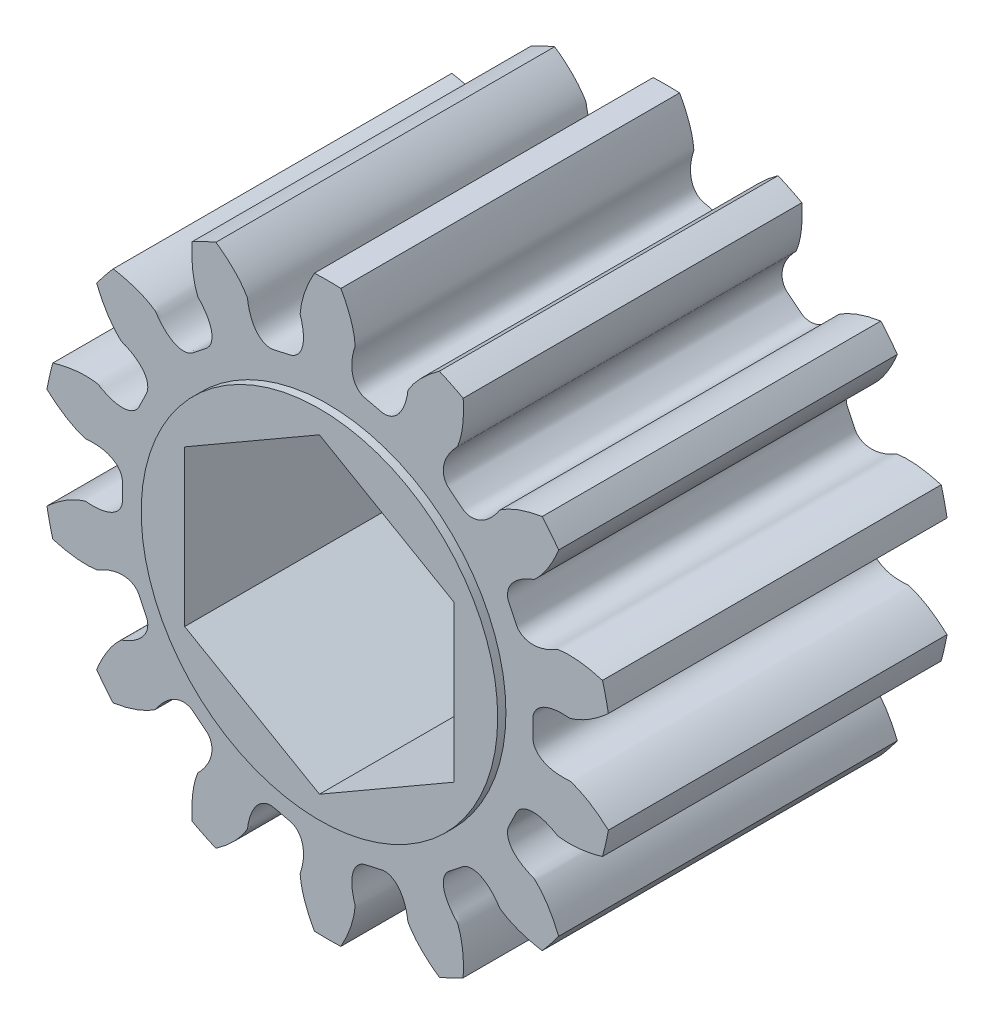
SolidWorks part; units mm, degrees
material "7075-T6 (SN)"
ref_plane "Front Plane" through (0, 0, 0) normal (0, 0, 1) x (1, 0, 0)
ref_plane "Top Plane" through (0, 0, 0) normal (0, 1, 0) x (1, 0, 0)
ref_plane "Right Plane" through (0, 0, 0) normal (1, 0, 0) x (0, 0, -1)
ref_plane "Plane1" through (0, 0, 6.0325) normal (0, 0, 1) x (1, 0, 0)
sketch "Sketch1" plane through (0, 0, 6.0325) normal (0, 0, 1) x (1, 0, 0)
  arc A0 (8.2288, 5.9593) -> (7.6409, 6.6964) centre (0, 0) ccw
  arc A1 (4.8282, 8.9394) -> (3.9788, 9.3485) centre (0, 0) ccw
  arc A2 (0.4714, 10.1491) -> (-0.4714, 10.1491) centre (0, 0) ccw
  arc A3 (-3.9788, 9.3485) -> (-4.8282, 8.9394) centre (0, 0) ccw
  arc A4 (-7.6409, 6.6964) -> (-8.2288, 5.9593) centre (0, 0) ccw
  arc A5 (-9.7897, 2.718) -> (-9.9995, 1.7988) centre (0, 0) ccw
  arc A6 (-9.9995, -1.7988) -> (-9.7897, -2.718) centre (0, 0) ccw
  arc A7 (-8.2288, -5.9593) -> (-7.6409, -6.6964) centre (0, 0) ccw
  arc A8 (-4.8282, -8.9394) -> (-3.9788, -9.3485) centre (0, 0) ccw
  arc A9 (-0.4714, -10.1491) -> (0.4714, -10.1491) centre (0, 0) ccw
  arc A10 (3.9788, -9.3485) -> (4.8282, -8.9394) centre (0, 0) ccw
  arc A11 (7.6409, -6.6964) -> (8.2288, -5.9593) centre (0, 0) ccw
  arc A12 (9.7897, -2.718) -> (9.9995, -1.7988) centre (0, 0) ccw
  arc A13 (9.9995, 1.7988) -> (9.7897, 2.718) centre (0, 0) ccw
  spline S0 degree 3 poles (8.2288, 5.9593) (8.1962, 5.8786) (8.1413, 5.7514) (8.0599, 5.5829) (7.9923, 5.4536) (7.9249, 5.3342) (7.8584, 5.2246) (7.7932, 5.1246) (7.7299, 5.0339) (7.669, 4.9525) (7.611, 4.8799) (7.5566, 4.8159) (7.506, 4.7604) (7.46, 4.7125) (7.4078, 4.6637) (7.3421, 4.5941) (7.241, 4.5723) (7.157, 4.5317) (7.0903, 4.5003) (7.0269, 4.467) (6.9663, 4.4327) (6.9087, 4.3974) (6.8539, 4.3609) (6.802, 4.3235) (6.7528, 4.2849) (6.7065, 4.2452) (6.663, 4.2044) (6.6223, 4.1622) (6.5843, 4.1185) (6.5492, 4.0731) (6.517, 4.0258) (6.4878, 3.9762) (6.4621, 3.9239) (6.4402, 3.8685) (6.4228, 3.8096) (6.4108, 3.7469) (6.4056, 3.6806) (6.4084, 3.6111) (6.4206, 3.5398) (6.4414, 3.4752) (6.4969, 3.3522) (6.5962, 3.1766) (6.6716, 2.9894) (6.7331, 2.8693) (6.7707, 2.8128) (6.8189, 2.7588) (6.8714, 2.7132) (6.9266, 2.676) (6.983, 2.6463) (7.0399, 2.6232) (7.0969, 2.6058) (7.1538, 2.5933) (7.2107, 2.5851) (7.2678, 2.5808) (7.3252, 2.58) (7.383, 2.5824) (7.4414, 2.588) (7.5005, 2.5965) (7.5604, 2.608) (7.6212, 2.6223) (7.6829, 2.6396) (7.7455, 2.6597) (7.8091, 2.6827) (7.8736, 2.7087) (7.9391, 2.7375) (8.0053, 2.77) (8.0894, 2.8104) (8.1695, 2.8759) (8.2649, 2.8839) (8.3356, 2.8943) (8.4017, 2.9003) (8.4767, 2.9053) (8.5607, 2.908) (8.6535, 2.908) (8.7552, 2.9048) (8.8655, 2.8978) (8.9844, 2.8865) (9.1115, 2.8702) (9.2469, 2.8484) (9.3901, 2.8206) (9.5727, 2.7791) (9.7064, 2.7428) (9.7897, 2.718) knots 0.010313 0.010313 0.010313 0.010313 0.046086 0.06731 0.087322 0.10612 0.123706 0.140079 0.155239 0.169186 0.18192 0.193442 0.203751 0.212847 0.22073 0.233282 0.251264 0.261667 0.271772 0.281588 0.291125 0.300395 0.30941 0.318185 0.326739 0.335092 0.343269 0.3513 0.35922 0.367069 0.374898 0.382761 0.390725 0.398861 0.407247 0.415956 0.425052 0.434567 0.444491 0.454753 0.462386 0.5 0.537614 0.545247 0.555509 0.565433 0.574948 0.584044 0.592753 0.601139 0.609275 0.617239 0.625102 0.632931 0.64078 0.6487 0.656731 0.664908 0.673261 0.681815 0.69059 0.699605 0.708875 0.718412 0.728228 0.738333 0.748736 0.766718 0.77927 0.787153 0.796249 0.806558 0.81808 0.830814 0.844761 0.859921 0.876294 0.89388 0.912678 0.93269 0.953914 0.989687 0.989687 0.989687 0.989687
  spline S1 degree 3 poles (4.8282, 8.9394) (4.8339, 8.8527) (4.8396, 8.7142) (4.8394, 8.5271) (4.8346, 8.3812) (4.8257, 8.2444) (4.8133, 8.1168) (4.7979, 7.9984) (4.7802, 7.8893) (4.7607, 7.7895) (4.74, 7.699) (4.7187, 7.6177) (4.6972, 7.5457) (4.6765, 7.4825) (4.6507, 7.4159) (4.6217, 7.3247) (4.54, 7.2612) (4.482, 7.1882) (4.4355, 7.1309) (4.3929, 7.0734) (4.3531, 7.0163) (4.3165, 6.9594) (4.283, 6.9029) (4.2525, 6.8466) (4.2249, 6.7905) (4.2004, 6.7347) (4.179, 6.679) (4.1606, 6.6233) (4.1453, 6.5675) (4.1333, 6.5113) (4.1248, 6.4547) (4.1201, 6.3974) (4.1196, 6.3391) (4.1239, 6.2797) (4.1338, 6.2191) (4.1502, 6.1574) (4.1743, 6.0954) (4.2069, 6.034) (4.2489, 5.975) (4.2956, 5.9259) (4.3991, 5.8391) (4.5647, 5.7239) (4.7138, 5.5881) (4.8214, 5.5066) (4.8797, 5.4719) (4.9466, 5.4441) (5.0137, 5.4259) (5.0795, 5.4163) (5.1433, 5.4141) (5.2046, 5.4179) (5.2634, 5.4269) (5.3202, 5.4404) (5.375, 5.4577) (5.4283, 5.4786) (5.4804, 5.5028) (5.5314, 5.5301) (5.5816, 5.5604) (5.6312, 5.5937) (5.6801, 5.6301) (5.7287, 5.6693) (5.7767, 5.7116) (5.8244, 5.7569) (5.8717, 5.8053) (5.9186, 5.8567) (5.9652, 5.9111) (6.0107, 5.9691) (6.0689, 6.042) (6.1127, 6.1357) (6.1951, 6.1843) (6.2543, 6.2243) (6.3113, 6.2585) (6.3767, 6.2955) (6.4512, 6.3343) (6.5348, 6.3747) (6.6278, 6.4159) (6.7302, 6.4575) (6.8422, 6.4988) (6.9639, 6.5393) (7.0953, 6.5784) (7.2364, 6.6155) (7.4188, 6.6573) (7.5551, 6.6826) (7.6409, 6.6964) knots 0.010313 0.010313 0.010313 0.010313 0.046086 0.06731 0.087322 0.10612 0.123706 0.140079 0.155239 0.169186 0.18192 0.193442 0.203751 0.212847 0.22073 0.233282 0.251264 0.261667 0.271772 0.281588 0.291125 0.300395 0.30941 0.318185 0.326739 0.335092 0.343269 0.3513 0.35922 0.367069 0.374898 0.382761 0.390725 0.398861 0.407247 0.415956 0.425052 0.434567 0.444491 0.454753 0.462386 0.5 0.537614 0.545247 0.555509 0.565433 0.574948 0.584044 0.592753 0.601139 0.609275 0.617239 0.625102 0.632931 0.64078 0.6487 0.656731 0.664908 0.673261 0.681815 0.69059 0.699605 0.708875 0.718412 0.728228 0.738333 0.748736 0.766718 0.77927 0.787153 0.796249 0.806558 0.81808 0.830814 0.844761 0.859921 0.876294 0.89388 0.912678 0.93269 0.953914 0.989687 0.989687 0.989687 0.989687
  spline S2 degree 3 poles (0.4714, 10.1491) (0.5141, 10.0733) (0.5793, 9.9511) (0.6604, 9.7823) (0.7193, 9.6489) (0.7707, 9.5218) (0.8149, 9.4014) (0.8524, 9.2881) (0.8838, 9.1821) (0.9095, 9.0837) (0.9301, 8.9931) (0.9462, 8.9106) (0.9581, 8.8365) (0.9669, 8.7706) (0.9725, 8.6994) (0.9859, 8.6046) (0.9399, 8.512) (0.9192, 8.421) (0.9023, 8.3492) (0.8888, 8.2789) (0.8778, 8.2102) (0.8695, 8.1431) (0.8638, 8.0776) (0.8607, 8.0136) (0.8602, 7.9512) (0.8624, 7.8903) (0.8672, 7.8307) (0.8748, 7.7726) (0.8853, 7.7157) (0.8988, 7.6599) (0.9158, 7.6052) (0.9364, 7.5515) (0.9612, 7.4988) (0.9909, 7.4471) (1.0261, 7.3968) (1.0676, 7.3484) (1.1162, 7.3029) (1.1722, 7.2618) (1.2357, 7.2268) (1.2991, 7.2028) (1.4299, 7.1695) (1.6291, 7.1376) (1.8224, 7.08) (1.9547, 7.0532) (2.0223, 7.0473) (2.0946, 7.0513) (2.163, 7.064) (2.2265, 7.0839) (2.2849, 7.1095) (2.3384, 7.1395) (2.3875, 7.1732) (2.4328, 7.21) (2.4747, 7.2494) (2.5137, 7.2913) (2.5501, 7.3357) (2.5842, 7.3824) (2.6163, 7.4315) (2.6465, 7.4831) (2.6748, 7.537) (2.7015, 7.5935) (2.7265, 7.6524) (2.7498, 7.7139) (2.7714, 7.778) (2.7913, 7.8447) (2.8097, 7.9139) (2.8255, 7.9859) (2.8464, 8.0769) (2.8451, 8.1803) (2.8983, 8.2598) (2.9343, 8.3216) (2.9708, 8.3771) (3.0137, 8.4388) (3.0639, 8.5061) (3.1218, 8.5787) (3.1877, 8.6562) (3.2619, 8.7381) (3.3449, 8.8239) (3.437, 8.9132) (3.5384, 9.0054) (3.6494, 9.1001) (3.7956, 9.217) (3.9074, 9.2988) (3.9788, 9.3485) knots 0.010313 0.010313 0.010313 0.010313 0.046086 0.06731 0.087322 0.10612 0.123706 0.140079 0.155239 0.169186 0.18192 0.193442 0.203751 0.212847 0.22073 0.233282 0.251264 0.261667 0.271772 0.281588 0.291125 0.300395 0.30941 0.318185 0.326739 0.335092 0.343269 0.3513 0.35922 0.367069 0.374898 0.382761 0.390725 0.398861 0.407247 0.415956 0.425052 0.434567 0.444491 0.454753 0.462386 0.5 0.537614 0.545247 0.555509 0.565433 0.574948 0.584044 0.592753 0.601139 0.609275 0.617239 0.625102 0.632931 0.64078 0.6487 0.656731 0.664908 0.673261 0.681815 0.69059 0.699605 0.708875 0.718412 0.728228 0.738333 0.748736 0.766718 0.77927 0.787153 0.796249 0.806558 0.81808 0.830814 0.844761 0.859921 0.876294 0.89388 0.912678 0.93269 0.953914 0.989687 0.989687 0.989687 0.989687
  spline S3 degree 3 poles (-3.9788, 9.3485) (-3.9074, 9.2988) (-3.7956, 9.217) (-3.6494, 9.1001) (-3.5384, 9.0054) (-3.437, 8.9132) (-3.3449, 8.8239) (-3.2619, 8.7381) (-3.1877, 8.6562) (-3.1218, 8.5787) (-3.0639, 8.5061) (-3.0137, 8.4388) (-2.9708, 8.3771) (-2.9343, 8.3216) (-2.8983, 8.2598) (-2.8451, 8.1803) (-2.8464, 8.0769) (-2.8255, 7.9859) (-2.8097, 7.9139) (-2.7913, 7.8447) (-2.7714, 7.778) (-2.7498, 7.7139) (-2.7265, 7.6524) (-2.7015, 7.5935) (-2.6748, 7.537) (-2.6465, 7.4831) (-2.6163, 7.4315) (-2.5842, 7.3824) (-2.5501, 7.3357) (-2.5137, 7.2913) (-2.4747, 7.2494) (-2.4328, 7.21) (-2.3875, 7.1732) (-2.3384, 7.1395) (-2.2849, 7.1095) (-2.2265, 7.0839) (-2.163, 7.064) (-2.0946, 7.0513) (-2.0223, 7.0473) (-1.9547, 7.0532) (-1.8224, 7.08) (-1.6291, 7.1376) (-1.4299, 7.1695) (-1.2991, 7.2028) (-1.2357, 7.2268) (-1.1722, 7.2618) (-1.1162, 7.3029) (-1.0676, 7.3484) (-1.0261, 7.3968) (-0.9909, 7.4471) (-0.9612, 7.4988) (-0.9364, 7.5515) (-0.9158, 7.6052) (-0.8988, 7.6599) (-0.8853, 7.7157) (-0.8748, 7.7726) (-0.8672, 7.8307) (-0.8624, 7.8903) (-0.8602, 7.9512) (-0.8607, 8.0136) (-0.8638, 8.0776) (-0.8695, 8.1431) (-0.8778, 8.2102) (-0.8888, 8.2789) (-0.9023, 8.3492) (-0.9192, 8.421) (-0.9399, 8.512) (-0.9859, 8.6046) (-0.9725, 8.6994) (-0.9669, 8.7706) (-0.9581, 8.8365) (-0.9462, 8.9106) (-0.9301, 8.9931) (-0.9095, 9.0837) (-0.8838, 9.1821) (-0.8524, 9.2881) (-0.8149, 9.4014) (-0.7707, 9.5218) (-0.7193, 9.6489) (-0.6604, 9.7823) (-0.5793, 9.9511) (-0.5141, 10.0733) (-0.4714, 10.1491) knots 0.010313 0.010313 0.010313 0.010313 0.046086 0.06731 0.087322 0.10612 0.123706 0.140079 0.155239 0.169186 0.18192 0.193442 0.203751 0.212847 0.22073 0.233282 0.251264 0.261667 0.271772 0.281588 0.291125 0.300395 0.30941 0.318185 0.326739 0.335092 0.343269 0.3513 0.35922 0.367069 0.374898 0.382761 0.390725 0.398861 0.407247 0.415956 0.425052 0.434567 0.444491 0.454753 0.462386 0.5 0.537614 0.545247 0.555509 0.565433 0.574948 0.584044 0.592753 0.601139 0.609275 0.617239 0.625102 0.632931 0.64078 0.6487 0.656731 0.664908 0.673261 0.681815 0.69059 0.699605 0.708875 0.718412 0.728228 0.738333 0.748736 0.766718 0.77927 0.787153 0.796249 0.806558 0.81808 0.830814 0.844761 0.859921 0.876294 0.89388 0.912678 0.93269 0.953914 0.989687 0.989687 0.989687 0.989687
  spline S4 degree 3 poles (-7.6409, 6.6964) (-7.5551, 6.6826) (-7.4188, 6.6573) (-7.2364, 6.6155) (-7.0953, 6.5784) (-6.9639, 6.5393) (-6.8422, 6.4988) (-6.7302, 6.4575) (-6.6278, 6.4159) (-6.5348, 6.3747) (-6.4512, 6.3343) (-6.3767, 6.2955) (-6.3113, 6.2585) (-6.2543, 6.2243) (-6.1951, 6.1843) (-6.1127, 6.1357) (-6.0689, 6.042) (-6.0107, 5.9691) (-5.9652, 5.9111) (-5.9186, 5.8567) (-5.8717, 5.8053) (-5.8244, 5.7569) (-5.7767, 5.7116) (-5.7287, 5.6693) (-5.6801, 5.6301) (-5.6312, 5.5937) (-5.5816, 5.5604) (-5.5314, 5.5301) (-5.4804, 5.5028) (-5.4283, 5.4786) (-5.375, 5.4577) (-5.3202, 5.4404) (-5.2634, 5.4269) (-5.2046, 5.4179) (-5.1433, 5.4141) (-5.0795, 5.4163) (-5.0137, 5.4259) (-4.9466, 5.4441) (-4.8797, 5.4719) (-4.8214, 5.5066) (-4.7138, 5.5881) (-4.5647, 5.7239) (-4.3991, 5.8391) (-4.2956, 5.9259) (-4.2489, 5.975) (-4.2069, 6.034) (-4.1743, 6.0954) (-4.1502, 6.1574) (-4.1338, 6.2191) (-4.1239, 6.2797) (-4.1196, 6.3391) (-4.1201, 6.3974) (-4.1248, 6.4547) (-4.1333, 6.5113) (-4.1453, 6.5675) (-4.1606, 6.6233) (-4.179, 6.679) (-4.2004, 6.7347) (-4.2249, 6.7905) (-4.2525, 6.8466) (-4.283, 6.9029) (-4.3165, 6.9594) (-4.3531, 7.0163) (-4.3929, 7.0734) (-4.4355, 7.1309) (-4.482, 7.1882) (-4.54, 7.2612) (-4.6217, 7.3247) (-4.6507, 7.4159) (-4.6765, 7.4825) (-4.6972, 7.5457) (-4.7187, 7.6177) (-4.74, 7.699) (-4.7607, 7.7895) (-4.7802, 7.8893) (-4.7979, 7.9984) (-4.8133, 8.1168) (-4.8257, 8.2444) (-4.8346, 8.3812) (-4.8394, 8.5271) (-4.8396, 8.7142) (-4.8339, 8.8527) (-4.8282, 8.9394) knots 0.010313 0.010313 0.010313 0.010313 0.046086 0.06731 0.087322 0.10612 0.123706 0.140079 0.155239 0.169186 0.18192 0.193442 0.203751 0.212847 0.22073 0.233282 0.251264 0.261667 0.271772 0.281588 0.291125 0.300395 0.30941 0.318185 0.326739 0.335092 0.343269 0.3513 0.35922 0.367069 0.374898 0.382761 0.390725 0.398861 0.407247 0.415956 0.425052 0.434567 0.444491 0.454753 0.462386 0.5 0.537614 0.545247 0.555509 0.565433 0.574948 0.584044 0.592753 0.601139 0.609275 0.617239 0.625102 0.632931 0.64078 0.6487 0.656731 0.664908 0.673261 0.681815 0.69059 0.699605 0.708875 0.718412 0.728228 0.738333 0.748736 0.766718 0.77927 0.787153 0.796249 0.806558 0.81808 0.830814 0.844761 0.859921 0.876294 0.89388 0.912678 0.93269 0.953914 0.989687 0.989687 0.989687 0.989687
  spline S5 degree 3 poles (-9.7897, 2.718) (-9.7064, 2.7428) (-9.5727, 2.7791) (-9.3901, 2.8206) (-9.2469, 2.8484) (-9.1115, 2.8702) (-8.9844, 2.8865) (-8.8655, 2.8978) (-8.7552, 2.9048) (-8.6535, 2.908) (-8.5607, 2.908) (-8.4767, 2.9053) (-8.4017, 2.9003) (-8.3356, 2.8943) (-8.2649, 2.8839) (-8.1695, 2.8759) (-8.0894, 2.8104) (-8.0053, 2.77) (-7.9391, 2.7375) (-7.8736, 2.7087) (-7.8091, 2.6827) (-7.7455, 2.6597) (-7.6829, 2.6396) (-7.6212, 2.6223) (-7.5604, 2.608) (-7.5005, 2.5965) (-7.4414, 2.588) (-7.383, 2.5824) (-7.3252, 2.58) (-7.2678, 2.5808) (-7.2107, 2.5851) (-7.1538, 2.5933) (-7.0969, 2.6058) (-7.0399, 2.6232) (-6.983, 2.6463) (-6.9266, 2.676) (-6.8714, 2.7132) (-6.8189, 2.7588) (-6.7707, 2.8128) (-6.7331, 2.8693) (-6.6716, 2.9894) (-6.5962, 3.1766) (-6.4969, 3.3522) (-6.4414, 3.4752) (-6.4206, 3.5398) (-6.4084, 3.6111) (-6.4056, 3.6806) (-6.4108, 3.7469) (-6.4228, 3.8096) (-6.4402, 3.8685) (-6.4621, 3.9239) (-6.4878, 3.9762) (-6.517, 4.0258) (-6.5492, 4.0731) (-6.5843, 4.1185) (-6.6223, 4.1622) (-6.663, 4.2044) (-6.7065, 4.2452) (-6.7528, 4.2849) (-6.802, 4.3235) (-6.8539, 4.3609) (-6.9087, 4.3974) (-6.9663, 4.4327) (-7.0269, 4.467) (-7.0903, 4.5003) (-7.157, 4.5317) (-7.241, 4.5723) (-7.3421, 4.5941) (-7.4078, 4.6637) (-7.46, 4.7125) (-7.506, 4.7604) (-7.5566, 4.8159) (-7.611, 4.8799) (-7.669, 4.9525) (-7.7299, 5.0339) (-7.7932, 5.1246) (-7.8584, 5.2246) (-7.9249, 5.3342) (-7.9923, 5.4536) (-8.0599, 5.5829) (-8.1413, 5.7514) (-8.1962, 5.8786) (-8.2288, 5.9593) knots 0.010313 0.010313 0.010313 0.010313 0.046086 0.06731 0.087322 0.10612 0.123706 0.140079 0.155239 0.169186 0.18192 0.193442 0.203751 0.212847 0.22073 0.233282 0.251264 0.261667 0.271772 0.281588 0.291125 0.300395 0.30941 0.318185 0.326739 0.335092 0.343269 0.3513 0.35922 0.367069 0.374898 0.382761 0.390725 0.398861 0.407247 0.415956 0.425052 0.434567 0.444491 0.454753 0.462386 0.5 0.537614 0.545247 0.555509 0.565433 0.574948 0.584044 0.592753 0.601139 0.609275 0.617239 0.625102 0.632931 0.64078 0.6487 0.656731 0.664908 0.673261 0.681815 0.69059 0.699605 0.708875 0.718412 0.728228 0.738333 0.748736 0.766718 0.77927 0.787153 0.796249 0.806558 0.81808 0.830814 0.844761 0.859921 0.876294 0.89388 0.912678 0.93269 0.953914 0.989687 0.989687 0.989687 0.989687
  spline S6 degree 3 poles (-9.9995, -1.7988) (-9.9352, -1.7403) (-9.8305, -1.6495) (-9.684, -1.5329) (-9.567, -1.4458) (-9.4545, -1.3674) (-9.347, -1.2976) (-9.2449, -1.2357) (-9.1485, -1.1816) (-9.0583, -1.1346) (-8.9746, -1.0943) (-8.8978, -1.0603) (-8.8281, -1.0323) (-8.7659, -1.009) (-8.6977, -0.9877) (-8.6083, -0.9535) (-8.5077, -0.9778) (-8.4144, -0.9777) (-8.3407, -0.9782) (-8.2691, -0.9757) (-8.1997, -0.9712) (-8.1324, -0.9643) (-8.0673, -0.9553) (-8.0042, -0.9441) (-7.9433, -0.9306) (-7.8843, -0.915) (-7.8274, -0.897) (-7.7724, -0.8767) (-7.7192, -0.8538) (-7.6679, -0.8282) (-7.6183, -0.7995) (-7.5705, -0.7674) (-7.5247, -0.7315) (-7.4809, -0.6911) (-7.4397, -0.6456) (-7.4017, -0.5943) (-7.3682, -0.5368) (-7.3406, -0.473) (-7.3206, -0.4034) (-7.3113, -0.3362) (-7.308, -0.2013) (-7.3212, 0) (-7.308, 0.2013) (-7.3113, 0.3362) (-7.3206, 0.4034) (-7.3406, 0.473) (-7.3682, 0.5368) (-7.4017, 0.5943) (-7.4397, 0.6456) (-7.4809, 0.6911) (-7.5247, 0.7315) (-7.5705, 0.7674) (-7.6183, 0.7995) (-7.6679, 0.8282) (-7.7192, 0.8538) (-7.7724, 0.8767) (-7.8274, 0.897) (-7.8843, 0.915) (-7.9433, 0.9306) (-8.0042, 0.9441) (-8.0673, 0.9553) (-8.1324, 0.9643) (-8.1997, 0.9712) (-8.2691, 0.9757) (-8.3407, 0.9782) (-8.4144, 0.9777) (-8.5077, 0.9778) (-8.6083, 0.9535) (-8.6977, 0.9877) (-8.7659, 1.009) (-8.8281, 1.0323) (-8.8978, 1.0603) (-8.9746, 1.0943) (-9.0583, 1.1346) (-9.1485, 1.1816) (-9.2449, 1.2357) (-9.347, 1.2976) (-9.4545, 1.3674) (-9.567, 1.4458) (-9.684, 1.5329) (-9.8305, 1.6495) (-9.9352, 1.7403) (-9.9995, 1.7988) knots 0.010313 0.010313 0.010313 0.010313 0.046086 0.06731 0.087322 0.10612 0.123706 0.140079 0.155239 0.169186 0.18192 0.193442 0.203751 0.212847 0.22073 0.233282 0.251264 0.261667 0.271772 0.281588 0.291125 0.300395 0.30941 0.318185 0.326739 0.335092 0.343269 0.3513 0.35922 0.367069 0.374898 0.382761 0.390725 0.398861 0.407247 0.415956 0.425052 0.434567 0.444491 0.454753 0.462386 0.5 0.537614 0.545247 0.555509 0.565433 0.574948 0.584044 0.592753 0.601139 0.609275 0.617239 0.625102 0.632931 0.64078 0.6487 0.656731 0.664908 0.673261 0.681815 0.69059 0.699605 0.708875 0.718412 0.728228 0.738333 0.748736 0.766718 0.77927 0.787153 0.796249 0.806558 0.81808 0.830814 0.844761 0.859921 0.876294 0.89388 0.912678 0.93269 0.953914 0.989687 0.989687 0.989687 0.989687
  spline S7 degree 3 poles (-8.2288, -5.9593) (-8.1962, -5.8786) (-8.1413, -5.7514) (-8.0599, -5.5829) (-7.9923, -5.4536) (-7.9249, -5.3342) (-7.8584, -5.2246) (-7.7932, -5.1246) (-7.7299, -5.0339) (-7.669, -4.9525) (-7.611, -4.8799) (-7.5566, -4.8159) (-7.506, -4.7604) (-7.46, -4.7125) (-7.4078, -4.6637) (-7.3421, -4.5941) (-7.241, -4.5723) (-7.157, -4.5317) (-7.0903, -4.5003) (-7.0269, -4.467) (-6.9663, -4.4327) (-6.9087, -4.3974) (-6.8539, -4.3609) (-6.802, -4.3235) (-6.7528, -4.2849) (-6.7065, -4.2452) (-6.663, -4.2044) (-6.6223, -4.1622) (-6.5843, -4.1185) (-6.5492, -4.0731) (-6.517, -4.0258) (-6.4878, -3.9762) (-6.4621, -3.9239) (-6.4402, -3.8685) (-6.4228, -3.8096) (-6.4108, -3.7469) (-6.4056, -3.6806) (-6.4084, -3.6111) (-6.4206, -3.5398) (-6.4414, -3.4752) (-6.4969, -3.3522) (-6.5962, -3.1766) (-6.6716, -2.9894) (-6.7331, -2.8693) (-6.7707, -2.8128) (-6.8189, -2.7588) (-6.8714, -2.7132) (-6.9266, -2.676) (-6.983, -2.6463) (-7.0399, -2.6232) (-7.0969, -2.6058) (-7.1538, -2.5933) (-7.2107, -2.5851) (-7.2678, -2.5808) (-7.3252, -2.58) (-7.383, -2.5824) (-7.4414, -2.588) (-7.5005, -2.5965) (-7.5604, -2.608) (-7.6212, -2.6223) (-7.6829, -2.6396) (-7.7455, -2.6597) (-7.8091, -2.6827) (-7.8736, -2.7087) (-7.9391, -2.7375) (-8.0053, -2.77) (-8.0894, -2.8104) (-8.1695, -2.8759) (-8.2649, -2.8839) (-8.3356, -2.8943) (-8.4017, -2.9003) (-8.4767, -2.9053) (-8.5607, -2.908) (-8.6535, -2.908) (-8.7552, -2.9048) (-8.8655, -2.8978) (-8.9844, -2.8865) (-9.1115, -2.8702) (-9.2469, -2.8484) (-9.3901, -2.8206) (-9.5727, -2.7791) (-9.7064, -2.7428) (-9.7897, -2.718) knots 0.010313 0.010313 0.010313 0.010313 0.046086 0.06731 0.087322 0.10612 0.123706 0.140079 0.155239 0.169186 0.18192 0.193442 0.203751 0.212847 0.22073 0.233282 0.251264 0.261667 0.271772 0.281588 0.291125 0.300395 0.30941 0.318185 0.326739 0.335092 0.343269 0.3513 0.35922 0.367069 0.374898 0.382761 0.390725 0.398861 0.407247 0.415956 0.425052 0.434567 0.444491 0.454753 0.462386 0.5 0.537614 0.545247 0.555509 0.565433 0.574948 0.584044 0.592753 0.601139 0.609275 0.617239 0.625102 0.632931 0.64078 0.6487 0.656731 0.664908 0.673261 0.681815 0.69059 0.699605 0.708875 0.718412 0.728228 0.738333 0.748736 0.766718 0.77927 0.787153 0.796249 0.806558 0.81808 0.830814 0.844761 0.859921 0.876294 0.89388 0.912678 0.93269 0.953914 0.989687 0.989687 0.989687 0.989687
  spline S8 degree 3 poles (-4.8282, -8.9394) (-4.8339, -8.8527) (-4.8396, -8.7142) (-4.8394, -8.5271) (-4.8346, -8.3812) (-4.8257, -8.2444) (-4.8133, -8.1168) (-4.7979, -7.9984) (-4.7802, -7.8893) (-4.7607, -7.7895) (-4.74, -7.699) (-4.7187, -7.6177) (-4.6972, -7.5457) (-4.6765, -7.4825) (-4.6507, -7.4159) (-4.6217, -7.3247) (-4.54, -7.2612) (-4.482, -7.1882) (-4.4355, -7.1309) (-4.3929, -7.0734) (-4.3531, -7.0163) (-4.3165, -6.9594) (-4.283, -6.9029) (-4.2525, -6.8466) (-4.2249, -6.7905) (-4.2004, -6.7347) (-4.179, -6.679) (-4.1606, -6.6233) (-4.1453, -6.5675) (-4.1333, -6.5113) (-4.1248, -6.4547) (-4.1201, -6.3974) (-4.1196, -6.3391) (-4.1239, -6.2797) (-4.1338, -6.2191) (-4.1502, -6.1574) (-4.1743, -6.0954) (-4.2069, -6.034) (-4.2489, -5.975) (-4.2956, -5.9259) (-4.3991, -5.8391) (-4.5647, -5.7239) (-4.7138, -5.5881) (-4.8214, -5.5066) (-4.8797, -5.4719) (-4.9466, -5.4441) (-5.0137, -5.4259) (-5.0795, -5.4163) (-5.1433, -5.4141) (-5.2046, -5.4179) (-5.2634, -5.4269) (-5.3202, -5.4404) (-5.375, -5.4577) (-5.4283, -5.4786) (-5.4804, -5.5028) (-5.5314, -5.5301) (-5.5816, -5.5604) (-5.6312, -5.5937) (-5.6801, -5.6301) (-5.7287, -5.6693) (-5.7767, -5.7116) (-5.8244, -5.7569) (-5.8717, -5.8053) (-5.9186, -5.8567) (-5.9652, -5.9111) (-6.0107, -5.9691) (-6.0689, -6.042) (-6.1127, -6.1357) (-6.1951, -6.1843) (-6.2543, -6.2243) (-6.3113, -6.2585) (-6.3767, -6.2955) (-6.4512, -6.3343) (-6.5348, -6.3747) (-6.6278, -6.4159) (-6.7302, -6.4575) (-6.8422, -6.4988) (-6.9639, -6.5393) (-7.0953, -6.5784) (-7.2364, -6.6155) (-7.4188, -6.6573) (-7.5551, -6.6826) (-7.6409, -6.6964) knots 0.010313 0.010313 0.010313 0.010313 0.046086 0.06731 0.087322 0.10612 0.123706 0.140079 0.155239 0.169186 0.18192 0.193442 0.203751 0.212847 0.22073 0.233282 0.251264 0.261667 0.271772 0.281588 0.291125 0.300395 0.30941 0.318185 0.326739 0.335092 0.343269 0.3513 0.35922 0.367069 0.374898 0.382761 0.390725 0.398861 0.407247 0.415956 0.425052 0.434567 0.444491 0.454753 0.462386 0.5 0.537614 0.545247 0.555509 0.565433 0.574948 0.584044 0.592753 0.601139 0.609275 0.617239 0.625102 0.632931 0.64078 0.6487 0.656731 0.664908 0.673261 0.681815 0.69059 0.699605 0.708875 0.718412 0.728228 0.738333 0.748736 0.766718 0.77927 0.787153 0.796249 0.806558 0.81808 0.830814 0.844761 0.859921 0.876294 0.89388 0.912678 0.93269 0.953914 0.989687 0.989687 0.989687 0.989687
  spline S9 degree 3 poles (-0.4714, -10.1491) (-0.5141, -10.0733) (-0.5793, -9.9511) (-0.6604, -9.7823) (-0.7193, -9.6489) (-0.7707, -9.5218) (-0.8149, -9.4014) (-0.8524, -9.2881) (-0.8838, -9.1821) (-0.9095, -9.0837) (-0.9301, -8.9931) (-0.9462, -8.9106) (-0.9581, -8.8365) (-0.9669, -8.7706) (-0.9725, -8.6994) (-0.9859, -8.6046) (-0.9399, -8.512) (-0.9192, -8.421) (-0.9023, -8.3492) (-0.8888, -8.2789) (-0.8778, -8.2102) (-0.8695, -8.1431) (-0.8638, -8.0776) (-0.8607, -8.0136) (-0.8602, -7.9512) (-0.8624, -7.8903) (-0.8672, -7.8307) (-0.8748, -7.7726) (-0.8853, -7.7157) (-0.8988, -7.6599) (-0.9158, -7.6052) (-0.9364, -7.5515) (-0.9612, -7.4988) (-0.9909, -7.4471) (-1.0261, -7.3968) (-1.0676, -7.3484) (-1.1162, -7.3029) (-1.1722, -7.2618) (-1.2357, -7.2268) (-1.2991, -7.2028) (-1.4299, -7.1695) (-1.6291, -7.1376) (-1.8224, -7.08) (-1.9547, -7.0532) (-2.0223, -7.0473) (-2.0946, -7.0513) (-2.163, -7.064) (-2.2265, -7.0839) (-2.2849, -7.1095) (-2.3384, -7.1395) (-2.3875, -7.1732) (-2.4328, -7.21) (-2.4747, -7.2494) (-2.5137, -7.2913) (-2.5501, -7.3357) (-2.5842, -7.3824) (-2.6163, -7.4315) (-2.6465, -7.4831) (-2.6748, -7.537) (-2.7015, -7.5935) (-2.7265, -7.6524) (-2.7498, -7.7139) (-2.7714, -7.778) (-2.7913, -7.8447) (-2.8097, -7.9139) (-2.8255, -7.9859) (-2.8464, -8.0769) (-2.8451, -8.1803) (-2.8983, -8.2598) (-2.9343, -8.3216) (-2.9708, -8.3771) (-3.0137, -8.4388) (-3.0639, -8.5061) (-3.1218, -8.5787) (-3.1877, -8.6562) (-3.2619, -8.7381) (-3.3449, -8.8239) (-3.437, -8.9132) (-3.5384, -9.0054) (-3.6494, -9.1001) (-3.7956, -9.217) (-3.9074, -9.2988) (-3.9788, -9.3485) knots 0.010313 0.010313 0.010313 0.010313 0.046086 0.06731 0.087322 0.10612 0.123706 0.140079 0.155239 0.169186 0.18192 0.193442 0.203751 0.212847 0.22073 0.233282 0.251264 0.261667 0.271772 0.281588 0.291125 0.300395 0.30941 0.318185 0.326739 0.335092 0.343269 0.3513 0.35922 0.367069 0.374898 0.382761 0.390725 0.398861 0.407247 0.415956 0.425052 0.434567 0.444491 0.454753 0.462386 0.5 0.537614 0.545247 0.555509 0.565433 0.574948 0.584044 0.592753 0.601139 0.609275 0.617239 0.625102 0.632931 0.64078 0.6487 0.656731 0.664908 0.673261 0.681815 0.69059 0.699605 0.708875 0.718412 0.728228 0.738333 0.748736 0.766718 0.77927 0.787153 0.796249 0.806558 0.81808 0.830814 0.844761 0.859921 0.876294 0.89388 0.912678 0.93269 0.953914 0.989687 0.989687 0.989687 0.989687
  spline S10 degree 3 poles (3.9788, -9.3485) (3.9074, -9.2988) (3.7956, -9.217) (3.6494, -9.1001) (3.5384, -9.0054) (3.437, -8.9132) (3.3449, -8.8239) (3.2619, -8.7381) (3.1877, -8.6562) (3.1218, -8.5787) (3.0639, -8.5061) (3.0137, -8.4388) (2.9708, -8.3771) (2.9343, -8.3216) (2.8983, -8.2598) (2.8451, -8.1803) (2.8464, -8.0769) (2.8255, -7.9859) (2.8097, -7.9139) (2.7913, -7.8447) (2.7714, -7.778) (2.7498, -7.7139) (2.7265, -7.6524) (2.7015, -7.5935) (2.6748, -7.537) (2.6465, -7.4831) (2.6163, -7.4315) (2.5842, -7.3824) (2.5501, -7.3357) (2.5137, -7.2913) (2.4747, -7.2494) (2.4328, -7.21) (2.3875, -7.1732) (2.3384, -7.1395) (2.2849, -7.1095) (2.2265, -7.0839) (2.163, -7.064) (2.0946, -7.0513) (2.0223, -7.0473) (1.9547, -7.0532) (1.8224, -7.08) (1.6291, -7.1376) (1.4299, -7.1695) (1.2991, -7.2028) (1.2357, -7.2268) (1.1722, -7.2618) (1.1162, -7.3029) (1.0676, -7.3484) (1.0261, -7.3968) (0.9909, -7.4471) (0.9612, -7.4988) (0.9364, -7.5515) (0.9158, -7.6052) (0.8988, -7.6599) (0.8853, -7.7157) (0.8748, -7.7726) (0.8672, -7.8307) (0.8624, -7.8903) (0.8602, -7.9512) (0.8607, -8.0136) (0.8638, -8.0776) (0.8695, -8.1431) (0.8778, -8.2102) (0.8888, -8.2789) (0.9023, -8.3492) (0.9192, -8.421) (0.9399, -8.512) (0.9859, -8.6046) (0.9725, -8.6994) (0.9669, -8.7706) (0.9581, -8.8365) (0.9462, -8.9106) (0.9301, -8.9931) (0.9095, -9.0837) (0.8838, -9.1821) (0.8524, -9.2881) (0.8149, -9.4014) (0.7707, -9.5218) (0.7193, -9.6489) (0.6604, -9.7823) (0.5793, -9.9511) (0.5141, -10.0733) (0.4714, -10.1491) knots 0.010313 0.010313 0.010313 0.010313 0.046086 0.06731 0.087322 0.10612 0.123706 0.140079 0.155239 0.169186 0.18192 0.193442 0.203751 0.212847 0.22073 0.233282 0.251264 0.261667 0.271772 0.281588 0.291125 0.300395 0.30941 0.318185 0.326739 0.335092 0.343269 0.3513 0.35922 0.367069 0.374898 0.382761 0.390725 0.398861 0.407247 0.415956 0.425052 0.434567 0.444491 0.454753 0.462386 0.5 0.537614 0.545247 0.555509 0.565433 0.574948 0.584044 0.592753 0.601139 0.609275 0.617239 0.625102 0.632931 0.64078 0.6487 0.656731 0.664908 0.673261 0.681815 0.69059 0.699605 0.708875 0.718412 0.728228 0.738333 0.748736 0.766718 0.77927 0.787153 0.796249 0.806558 0.81808 0.830814 0.844761 0.859921 0.876294 0.89388 0.912678 0.93269 0.953914 0.989687 0.989687 0.989687 0.989687
  spline S11 degree 3 poles (7.6409, -6.6964) (7.5551, -6.6826) (7.4188, -6.6573) (7.2364, -6.6155) (7.0953, -6.5784) (6.9639, -6.5393) (6.8422, -6.4988) (6.7302, -6.4575) (6.6278, -6.4159) (6.5348, -6.3747) (6.4512, -6.3343) (6.3767, -6.2955) (6.3113, -6.2585) (6.2543, -6.2243) (6.1951, -6.1843) (6.1127, -6.1357) (6.0689, -6.042) (6.0107, -5.9691) (5.9652, -5.9111) (5.9186, -5.8567) (5.8717, -5.8053) (5.8244, -5.7569) (5.7767, -5.7116) (5.7287, -5.6693) (5.6801, -5.6301) (5.6312, -5.5937) (5.5816, -5.5604) (5.5314, -5.5301) (5.4804, -5.5028) (5.4283, -5.4786) (5.375, -5.4577) (5.3202, -5.4404) (5.2634, -5.4269) (5.2046, -5.4179) (5.1433, -5.4141) (5.0795, -5.4163) (5.0137, -5.4259) (4.9466, -5.4441) (4.8797, -5.4719) (4.8214, -5.5066) (4.7138, -5.5881) (4.5647, -5.7239) (4.3991, -5.8391) (4.2956, -5.9259) (4.2489, -5.975) (4.2069, -6.034) (4.1743, -6.0954) (4.1502, -6.1574) (4.1338, -6.2191) (4.1239, -6.2797) (4.1196, -6.3391) (4.1201, -6.3974) (4.1248, -6.4547) (4.1333, -6.5113) (4.1453, -6.5675) (4.1606, -6.6233) (4.179, -6.679) (4.2004, -6.7347) (4.2249, -6.7905) (4.2525, -6.8466) (4.283, -6.9029) (4.3165, -6.9594) (4.3531, -7.0163) (4.3929, -7.0734) (4.4355, -7.1309) (4.482, -7.1882) (4.54, -7.2612) (4.6217, -7.3247) (4.6507, -7.4159) (4.6765, -7.4825) (4.6972, -7.5457) (4.7187, -7.6177) (4.74, -7.699) (4.7607, -7.7895) (4.7802, -7.8893) (4.7979, -7.9984) (4.8133, -8.1168) (4.8257, -8.2444) (4.8346, -8.3812) (4.8394, -8.5271) (4.8396, -8.7142) (4.8339, -8.8527) (4.8282, -8.9394) knots 0.010313 0.010313 0.010313 0.010313 0.046086 0.06731 0.087322 0.10612 0.123706 0.140079 0.155239 0.169186 0.18192 0.193442 0.203751 0.212847 0.22073 0.233282 0.251264 0.261667 0.271772 0.281588 0.291125 0.300395 0.30941 0.318185 0.326739 0.335092 0.343269 0.3513 0.35922 0.367069 0.374898 0.382761 0.390725 0.398861 0.407247 0.415956 0.425052 0.434567 0.444491 0.454753 0.462386 0.5 0.537614 0.545247 0.555509 0.565433 0.574948 0.584044 0.592753 0.601139 0.609275 0.617239 0.625102 0.632931 0.64078 0.6487 0.656731 0.664908 0.673261 0.681815 0.69059 0.699605 0.708875 0.718412 0.728228 0.738333 0.748736 0.766718 0.77927 0.787153 0.796249 0.806558 0.81808 0.830814 0.844761 0.859921 0.876294 0.89388 0.912678 0.93269 0.953914 0.989687 0.989687 0.989687 0.989687
  spline S12 degree 3 poles (9.7897, -2.718) (9.7064, -2.7428) (9.5727, -2.7791) (9.3901, -2.8206) (9.2469, -2.8484) (9.1115, -2.8702) (8.9844, -2.8865) (8.8655, -2.8978) (8.7552, -2.9048) (8.6535, -2.908) (8.5607, -2.908) (8.4767, -2.9053) (8.4017, -2.9003) (8.3356, -2.8943) (8.2649, -2.8839) (8.1695, -2.8759) (8.0894, -2.8104) (8.0053, -2.77) (7.9391, -2.7375) (7.8736, -2.7087) (7.8091, -2.6827) (7.7455, -2.6597) (7.6829, -2.6396) (7.6212, -2.6223) (7.5604, -2.608) (7.5005, -2.5965) (7.4414, -2.588) (7.383, -2.5824) (7.3252, -2.58) (7.2678, -2.5808) (7.2107, -2.5851) (7.1538, -2.5933) (7.0969, -2.6058) (7.0399, -2.6232) (6.983, -2.6463) (6.9266, -2.676) (6.8714, -2.7132) (6.8189, -2.7588) (6.7707, -2.8128) (6.7331, -2.8693) (6.6716, -2.9894) (6.5962, -3.1766) (6.4969, -3.3522) (6.4414, -3.4752) (6.4206, -3.5398) (6.4084, -3.6111) (6.4056, -3.6806) (6.4108, -3.7469) (6.4228, -3.8096) (6.4402, -3.8685) (6.4621, -3.9239) (6.4878, -3.9762) (6.517, -4.0258) (6.5492, -4.0731) (6.5843, -4.1185) (6.6223, -4.1622) (6.663, -4.2044) (6.7065, -4.2452) (6.7528, -4.2849) (6.802, -4.3235) (6.8539, -4.3609) (6.9087, -4.3974) (6.9663, -4.4327) (7.0269, -4.467) (7.0903, -4.5003) (7.157, -4.5317) (7.241, -4.5723) (7.3421, -4.5941) (7.4078, -4.6637) (7.46, -4.7125) (7.506, -4.7604) (7.5566, -4.8159) (7.611, -4.8799) (7.669, -4.9525) (7.7299, -5.0339) (7.7932, -5.1246) (7.8584, -5.2246) (7.9249, -5.3342) (7.9923, -5.4536) (8.0599, -5.5829) (8.1413, -5.7514) (8.1962, -5.8786) (8.2288, -5.9593) knots 0.010313 0.010313 0.010313 0.010313 0.046086 0.06731 0.087322 0.10612 0.123706 0.140079 0.155239 0.169186 0.18192 0.193442 0.203751 0.212847 0.22073 0.233282 0.251264 0.261667 0.271772 0.281588 0.291125 0.300395 0.30941 0.318185 0.326739 0.335092 0.343269 0.3513 0.35922 0.367069 0.374898 0.382761 0.390725 0.398861 0.407247 0.415956 0.425052 0.434567 0.444491 0.454753 0.462386 0.5 0.537614 0.545247 0.555509 0.565433 0.574948 0.584044 0.592753 0.601139 0.609275 0.617239 0.625102 0.632931 0.64078 0.6487 0.656731 0.664908 0.673261 0.681815 0.69059 0.699605 0.708875 0.718412 0.728228 0.738333 0.748736 0.766718 0.77927 0.787153 0.796249 0.806558 0.81808 0.830814 0.844761 0.859921 0.876294 0.89388 0.912678 0.93269 0.953914 0.989687 0.989687 0.989687 0.989687
  spline S13 degree 3 poles (9.9995, 1.7988) (9.9352, 1.7403) (9.8305, 1.6495) (9.684, 1.5329) (9.567, 1.4458) (9.4545, 1.3674) (9.347, 1.2976) (9.2449, 1.2357) (9.1485, 1.1816) (9.0583, 1.1346) (8.9746, 1.0943) (8.8978, 1.0603) (8.8281, 1.0323) (8.7659, 1.009) (8.6977, 0.9877) (8.6083, 0.9535) (8.5077, 0.9778) (8.4144, 0.9777) (8.3407, 0.9782) (8.2691, 0.9757) (8.1997, 0.9712) (8.1324, 0.9643) (8.0673, 0.9553) (8.0042, 0.9441) (7.9433, 0.9306) (7.8843, 0.915) (7.8274, 0.897) (7.7724, 0.8767) (7.7192, 0.8538) (7.6679, 0.8282) (7.6183, 0.7995) (7.5705, 0.7674) (7.5247, 0.7315) (7.4809, 0.6911) (7.4397, 0.6456) (7.4017, 0.5943) (7.3682, 0.5368) (7.3406, 0.473) (7.3206, 0.4034) (7.3113, 0.3362) (7.308, 0.2013) (7.3212, 0) (7.308, -0.2013) (7.3113, -0.3362) (7.3206, -0.4034) (7.3406, -0.473) (7.3682, -0.5368) (7.4017, -0.5943) (7.4397, -0.6456) (7.4809, -0.6911) (7.5247, -0.7315) (7.5705, -0.7674) (7.6183, -0.7995) (7.6679, -0.8282) (7.7192, -0.8538) (7.7724, -0.8767) (7.8274, -0.897) (7.8843, -0.915) (7.9433, -0.9306) (8.0042, -0.9441) (8.0673, -0.9553) (8.1324, -0.9643) (8.1997, -0.9712) (8.2691, -0.9757) (8.3407, -0.9782) (8.4144, -0.9777) (8.5077, -0.9778) (8.6083, -0.9535) (8.6977, -0.9877) (8.7659, -1.009) (8.8281, -1.0323) (8.8978, -1.0603) (8.9746, -1.0943) (9.0583, -1.1346) (9.1485, -1.1816) (9.2449, -1.2357) (9.347, -1.2976) (9.4545, -1.3674) (9.567, -1.4458) (9.684, -1.5329) (9.8305, -1.6495) (9.9352, -1.7403) (9.9995, -1.7988) knots 0.010313 0.010313 0.010313 0.010313 0.046086 0.06731 0.087322 0.10612 0.123706 0.140079 0.155239 0.169186 0.18192 0.193442 0.203751 0.212847 0.22073 0.233282 0.251264 0.261667 0.271772 0.281588 0.291125 0.300395 0.30941 0.318185 0.326739 0.335092 0.343269 0.3513 0.35922 0.367069 0.374898 0.382761 0.390725 0.398861 0.407247 0.415956 0.425052 0.434567 0.444491 0.454753 0.462386 0.5 0.537614 0.545247 0.555509 0.565433 0.574948 0.584044 0.592753 0.601139 0.609275 0.617239 0.625102 0.632931 0.64078 0.6487 0.656731 0.664908 0.673261 0.681815 0.69059 0.699605 0.708875 0.718412 0.728228 0.738333 0.748736 0.766718 0.77927 0.787153 0.796249 0.806558 0.81808 0.830814 0.844761 0.859921 0.876294 0.89388 0.912678 0.93269 0.953914 0.989687 0.989687 0.989687 0.989687
extrude "Boss-Extrude1" add sketch "Sketch1" against normal blind 12.065
sketch "Sketch2" plane through (0, 0, 6.0325) normal (0, 0, 1) x (1, 0, 0)
  circle A0 centre (0, 0) radius 6.35
extrude "Boss-Extrude2" add sketch "Sketch2" along normal blind 0.2921
sketch "Sketch3" plane through (0, 0, -6.0325) normal (0, 0, -1) x (-1, 0, 0)
  circle A0 centre (0, 0) radius 6.35
extrude "Boss-Extrude3" add sketch "Sketch3" along normal blind 0.2921
sketch "Sketch4" plane through (0, 0, -6.3246) normal (0, 0, -1) x (-1, 0, 0)
  line L0 (-4.8006, 2.7716) -> (-4.8006, -2.7716)
  line L1 (-4.8006, -2.7716) -> (0, -5.5433)
  line L2 (0, -5.5433) -> (4.8006, -2.7716)
  line L3 (4.8006, -2.7716) -> (4.8006, 2.7716)
  line L4 (4.8006, 2.7716) -> (0, 5.5433)
  line L5 (0, 5.5433) -> (-4.8006, 2.7716)
extrude "Cut-Extrude1" cut sketch "Sketch4" against normal through all
